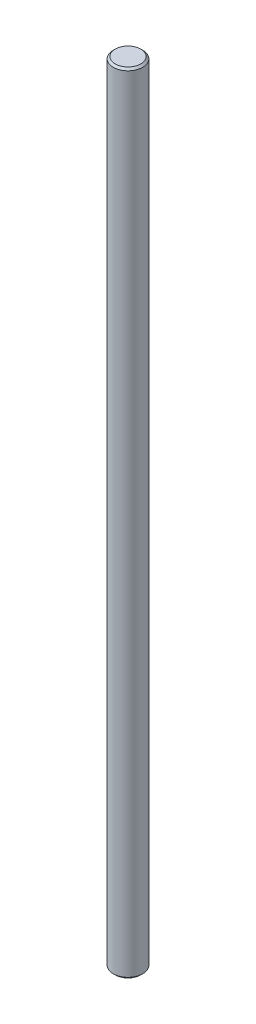
SolidWorks part; units mm, degrees
ref_plane "Front Plane" through (0, 0, 0) normal (0, 0, 1) x (1, 0, 0)
ref_plane "Top Plane" through (0, 0, 0) normal (0, 1, 0) x (1, 0, 0)
ref_plane "Right Plane" through (0, 0, 0) normal (1, 0, 0) x (0, 0, -1)
sketch "Sketch1" plane through (0, 0, 0) normal (0, 1, 0) x (1, 0, 0)
  circle A0 centre (0, 0) radius 4.7625
extrude "Boss-Extrude1" add sketch "Sketch1" along normal blind 254
chamfer "Chamfer1" distance 0.635 angle 45 2 edges at (0, 254, 4.7625) (0, 0, 4.7625)
